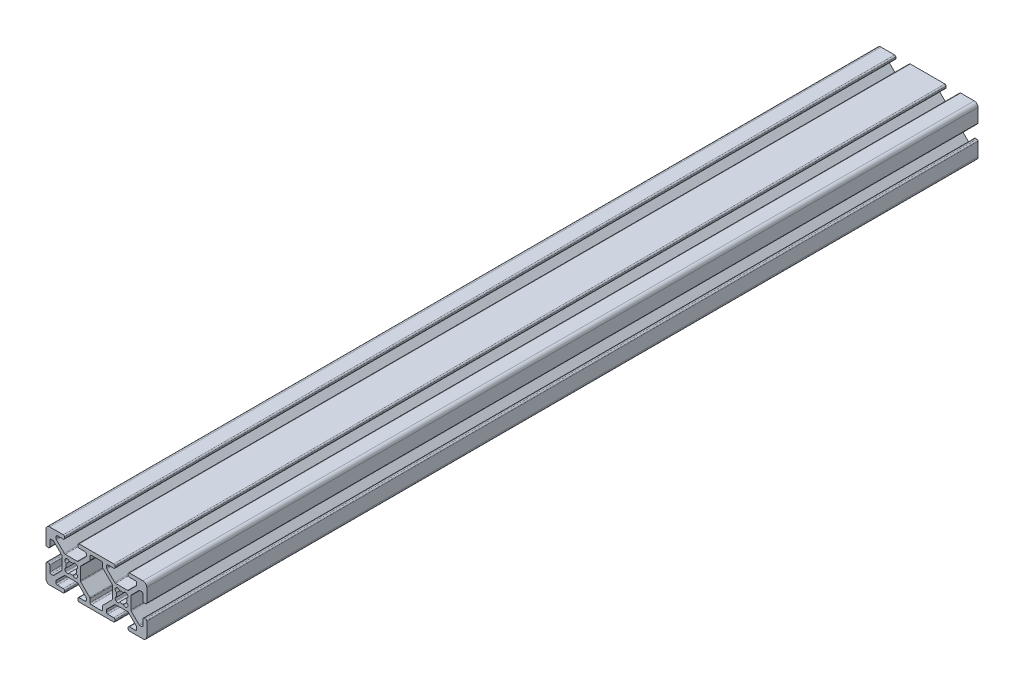
SolidWorks part; units mm, degrees
material "6105-T5 Aluminum"
ref_plane "Front Plane" through (0, 0, 0) normal (0, 0, 1) x (1, 0, 0)
ref_plane "Top Plane" through (0, 0, 0) normal (0, 1, 0) x (1, 0, 0)
ref_plane "Right Plane" through (0, 0, 0) normal (1, 0, 0) x (0, 0, -1)
sketch "Sketch1" plane through (0, 0, 0) normal (0, 0, 1) x (1, 0, 0)
  line L0 (-2.1249, -2.3045) -> (-2.3045, -2.1249)
  line L1 (-2.3045, 2.1249) -> (-2.1249, 2.3045)
  line L2 (2.1249, 2.3045) -> (2.3045, 2.1249)
  line L3 (2.3045, -2.1249) -> (2.1249, -2.3045)
  line L4 (-12.505, -7.992) -> (-12.505, -6.6448)
  line L5 (-12.6538, -6.2856) -> (-16.1962, -2.7431)
  line L6 (-16.345, -2.3839) -> (-16.345, 2.3839)
  line L7 (-16.1962, 2.7431) -> (-12.6538, 6.2856)
  line L8 (-12.505, 6.6448) -> (-12.505, 7.992)
  line L9 (-11.997, 8.5) -> (-8.003, 8.5)
  line L10 (-7.495, 7.992) -> (-7.495, 6.6448)
  line L11 (-7.3462, 6.2856) -> (-3.8038, 2.7431)
  line L12 (-3.655, 2.3839) -> (-3.655, -2.3839)
  line L13 (-3.8038, -2.7431) -> (-7.3462, -6.2856)
  line L14 (-7.495, -6.6448) -> (-7.495, -7.992)
  line L15 (-8.003, -8.5) -> (-11.997, -8.5)
  line L16 (-22.1249, -2.3045) -> (-22.3045, -2.1249)
  line L17 (-22.3045, 2.1249) -> (-22.1249, 2.3045)
  line L18 (-17.8751, 2.3045) -> (-17.6955, 2.1249)
  line L19 (-17.6955, -2.1249) -> (-17.8751, -2.3045)
  line L20 (-22.3839, -3.655) -> (-17.6161, -3.655)
  line L21 (-17.2569, -3.8038) -> (-14.1538, -6.9069)
  line L22 (-14.005, -7.2661) -> (-14.005, -7.992)
  line L23 (-14.513, -8.5) -> (-16.862, -8.5)
  line L24 (-17.37, -9.008) -> (-17.37, -9.492)
  line L25 (-16.862, -10) -> (-3.138, -10)
  line L26 (-2.63, -9.492) -> (-2.63, -9.008)
  line L27 (-3.138, -8.5) -> (-5.487, -8.5)
  line L28 (-5.995, -7.992) -> (-5.995, -7.2661)
  line L29 (-5.8462, -6.9069) -> (-2.7431, -3.8038)
  line L30 (-2.3839, -3.655) -> (2.3839, -3.655)
  line L31 (2.7431, -3.8038) -> (5.8462, -6.9069)
  line L32 (5.995, -7.2661) -> (5.995, -7.992)
  line L33 (5.487, -8.5) -> (3.138, -8.5)
  line L34 (2.63, -9.008) -> (2.63, -9.492)
  line L35 (3.138, -10) -> (8.5, -10)
  line L36 (10, -8.5) -> (10, -3.138)
  line L37 (9.492, -2.63) -> (9.008, -2.63)
  line L38 (8.5, -3.138) -> (8.5, -5.487)
  line L39 (7.992, -5.995) -> (7.2661, -5.995)
  line L40 (6.9069, -5.8462) -> (3.8038, -2.7431)
  line L41 (3.655, -2.3839) -> (3.655, 2.3839)
  line L42 (3.8038, 2.7431) -> (6.9069, 5.8462)
  line L43 (7.2661, 5.995) -> (7.992, 5.995)
  line L44 (8.5, 5.487) -> (8.5, 3.138)
  line L45 (9.008, 2.63) -> (9.492, 2.63)
  line L46 (10, 3.138) -> (10, 8.5)
  line L47 (8.5, 10) -> (3.138, 10)
  line L48 (2.63, 9.492) -> (2.63, 9.008)
  line L49 (3.138, 8.5) -> (5.487, 8.5)
  line L50 (5.995, 7.992) -> (5.995, 7.2661)
  line L51 (5.8462, 6.9069) -> (2.7431, 3.8038)
  line L52 (2.3839, 3.655) -> (-2.3839, 3.655)
  line L53 (-2.7431, 3.8038) -> (-5.8462, 6.9069)
  line L54 (-5.995, 7.2661) -> (-5.995, 7.992)
  line L55 (-5.487, 8.5) -> (-3.138, 8.5)
  line L56 (-2.63, 9.008) -> (-2.63, 9.492)
  line L57 (-3.138, 10) -> (-16.862, 10)
  line L58 (-17.37, 9.492) -> (-17.37, 9.008)
  line L59 (-16.862, 8.5) -> (-14.513, 8.5)
  line L60 (-14.005, 7.992) -> (-14.005, 7.2661)
  line L61 (-14.1538, 6.9069) -> (-17.2569, 3.8038)
  line L62 (-17.6161, 3.655) -> (-22.3839, 3.655)
  line L63 (-22.7431, 3.8038) -> (-25.8462, 6.9069)
  line L64 (-25.995, 7.2661) -> (-25.995, 7.992)
  line L65 (-25.487, 8.5) -> (-23.138, 8.5)
  line L66 (-22.63, 9.008) -> (-22.63, 9.492)
  line L67 (-23.138, 10) -> (-28.5, 10)
  line L68 (-30, 8.5) -> (-30, 3.138)
  line L69 (-29.492, 2.63) -> (-29.008, 2.63)
  line L70 (-28.5, 3.138) -> (-28.5, 5.487)
  line L71 (-27.992, 5.995) -> (-27.2661, 5.995)
  line L72 (-26.9069, 5.8462) -> (-23.8038, 2.7431)
  line L73 (-23.655, 2.3839) -> (-23.655, -2.3839)
  line L74 (-23.8038, -2.7431) -> (-26.9069, -5.8462)
  line L75 (-27.2661, -5.995) -> (-27.992, -5.995)
  line L76 (-28.5, -5.487) -> (-28.5, -3.138)
  line L77 (-29.008, -2.63) -> (-29.492, -2.63)
  line L78 (-30, -3.138) -> (-30, -8.5)
  line L79 (-28.5, -10) -> (-23.138, -10)
  line L80 (-22.63, -9.492) -> (-22.63, -9.008)
  line L81 (-23.138, -8.5) -> (-25.487, -8.5)
  line L82 (-25.995, -7.992) -> (-25.995, -7.2661)
  line L83 (-25.8462, -6.9069) -> (-22.7431, -3.8038)
  arc A0 (-1.9351, -0.804) -> (-2.3045, -2.1249) centre (-1.748, -1.5684) ccw
  arc A1 (-1.9351, 0.804) -> (-1.9351, -0.804) centre (0, 0) ccw
  arc A2 (-2.3045, 2.1249) -> (-1.9351, 0.804) centre (-1.748, 1.5684) ccw
  arc A3 (-0.804, 1.9351) -> (-2.1249, 2.3045) centre (-1.5684, 1.748) ccw
  arc A4 (0.804, 1.9351) -> (-0.804, 1.9351) centre (0, 0) ccw
  arc A5 (2.1249, 2.3045) -> (0.804, 1.9351) centre (1.5684, 1.748) ccw
  arc A6 (1.9351, 0.804) -> (2.3045, 2.1249) centre (1.748, 1.5684) ccw
  arc A7 (1.9351, -0.804) -> (1.9351, 0.804) centre (0, 0) ccw
  arc A8 (2.3045, -2.1249) -> (1.9351, -0.804) centre (1.748, -1.5684) ccw
  arc A9 (0.804, -1.9351) -> (2.1249, -2.3045) centre (1.5684, -1.748) ccw
  arc A10 (-0.804, -1.9351) -> (0.804, -1.9351) centre (0, 0) ccw
  arc A11 (-2.1249, -2.3045) -> (-0.804, -1.9351) centre (-1.5684, -1.748) ccw
  arc A12 (-12.505, -7.992) -> (-11.997, -8.5) centre (-11.997, -7.992) ccw
  arc A13 (-12.505, -6.6448) -> (-12.6538, -6.2856) centre (-13.013, -6.6448) ccw
  arc A14 (-16.345, -2.3839) -> (-16.1962, -2.7431) centre (-15.837, -2.3839) ccw
  arc A15 (-16.1962, 2.7431) -> (-16.345, 2.3839) centre (-15.837, 2.3839) ccw
  arc A16 (-12.6538, 6.2856) -> (-12.505, 6.6448) centre (-13.013, 6.6448) ccw
  arc A17 (-11.997, 8.5) -> (-12.505, 7.992) centre (-11.997, 7.992) ccw
  arc A18 (-7.495, 7.992) -> (-8.003, 8.5) centre (-8.003, 7.992) ccw
  arc A19 (-7.495, 6.6448) -> (-7.3462, 6.2856) centre (-6.987, 6.6448) ccw
  arc A20 (-3.655, 2.3839) -> (-3.8038, 2.7431) centre (-4.163, 2.3839) ccw
  arc A21 (-3.8038, -2.7431) -> (-3.655, -2.3839) centre (-4.163, -2.3839) ccw
  arc A22 (-7.3462, -6.2856) -> (-7.495, -6.6448) centre (-6.987, -6.6448) ccw
  arc A23 (-8.003, -8.5) -> (-7.495, -7.992) centre (-8.003, -7.992) ccw
  arc A24 (-21.9351, -0.804) -> (-22.3045, -2.1249) centre (-21.748, -1.5684) ccw
  arc A25 (-21.9351, 0.804) -> (-21.9351, -0.804) centre (-20, 0) ccw
  arc A26 (-22.3045, 2.1249) -> (-21.9351, 0.804) centre (-21.748, 1.5684) ccw
  arc A27 (-20.804, 1.9351) -> (-22.1249, 2.3045) centre (-21.5684, 1.748) ccw
  arc A28 (-19.196, 1.9351) -> (-20.804, 1.9351) centre (-20, 0) ccw
  arc A29 (-17.8751, 2.3045) -> (-19.196, 1.9351) centre (-18.4316, 1.748) ccw
  arc A30 (-18.0649, 0.804) -> (-17.6955, 2.1249) centre (-18.252, 1.5684) ccw
  arc A31 (-18.0649, -0.804) -> (-18.0649, 0.804) centre (-20, 0) ccw
  arc A32 (-17.6955, -2.1249) -> (-18.0649, -0.804) centre (-18.252, -1.5684) ccw
  arc A33 (-19.196, -1.9351) -> (-17.8751, -2.3045) centre (-18.4316, -1.748) ccw
  arc A34 (-20.804, -1.9351) -> (-19.196, -1.9351) centre (-20, 0) ccw
  arc A35 (-22.1249, -2.3045) -> (-20.804, -1.9351) centre (-21.5684, -1.748) ccw
  arc A36 (-22.3839, -3.655) -> (-22.7431, -3.8038) centre (-22.3839, -4.163) ccw
  arc A37 (-17.2569, -3.8038) -> (-17.6161, -3.655) centre (-17.6161, -4.163) ccw
  arc A38 (-14.005, -7.2661) -> (-14.1538, -6.9069) centre (-14.513, -7.2661) ccw
  arc A39 (-14.513, -8.5) -> (-14.005, -7.992) centre (-14.513, -7.992) ccw
  arc A40 (-16.862, -8.5) -> (-17.37, -9.008) centre (-16.862, -9.008) ccw
  arc A41 (-17.37, -9.492) -> (-16.862, -10) centre (-16.862, -9.492) ccw
  arc A42 (-3.138, -10) -> (-2.63, -9.492) centre (-3.138, -9.492) ccw
  arc A43 (-2.63, -9.008) -> (-3.138, -8.5) centre (-3.138, -9.008) ccw
  arc A44 (-5.995, -7.992) -> (-5.487, -8.5) centre (-5.487, -7.992) ccw
  arc A45 (-5.8462, -6.9069) -> (-5.995, -7.2661) centre (-5.487, -7.2661) ccw
  arc A46 (-2.3839, -3.655) -> (-2.7431, -3.8038) centre (-2.3839, -4.163) ccw
  arc A47 (2.7431, -3.8038) -> (2.3839, -3.655) centre (2.3839, -4.163) ccw
  arc A48 (5.995, -7.2661) -> (5.8462, -6.9069) centre (5.487, -7.2661) ccw
  arc A49 (5.487, -8.5) -> (5.995, -7.992) centre (5.487, -7.992) ccw
  arc A50 (3.138, -8.5) -> (2.63, -9.008) centre (3.138, -9.008) ccw
  arc A51 (2.63, -9.492) -> (3.138, -10) centre (3.138, -9.492) ccw
  arc A52 (8.5, -10) -> (10, -8.5) centre (8.5, -8.5) ccw
  arc A53 (10, -3.138) -> (9.492, -2.63) centre (9.492, -3.138) ccw
  arc A54 (9.008, -2.63) -> (8.5, -3.138) centre (9.008, -3.138) ccw
  arc A55 (7.992, -5.995) -> (8.5, -5.487) centre (7.992, -5.487) ccw
  arc A56 (6.9069, -5.8462) -> (7.2661, -5.995) centre (7.2661, -5.487) ccw
  arc A57 (3.655, -2.3839) -> (3.8038, -2.7431) centre (4.163, -2.3839) ccw
  arc A58 (3.8038, 2.7431) -> (3.655, 2.3839) centre (4.163, 2.3839) ccw
  arc A59 (7.2661, 5.995) -> (6.9069, 5.8462) centre (7.2661, 5.487) ccw
  arc A60 (8.5, 5.487) -> (7.992, 5.995) centre (7.992, 5.487) ccw
  arc A61 (8.5, 3.138) -> (9.008, 2.63) centre (9.008, 3.138) ccw
  arc A62 (9.492, 2.63) -> (10, 3.138) centre (9.492, 3.138) ccw
  arc A63 (10, 8.5) -> (8.5, 10) centre (8.5, 8.5) ccw
  arc A64 (3.138, 10) -> (2.63, 9.492) centre (3.138, 9.492) ccw
  arc A65 (2.63, 9.008) -> (3.138, 8.5) centre (3.138, 9.008) ccw
  arc A66 (5.995, 7.992) -> (5.487, 8.5) centre (5.487, 7.992) ccw
  arc A67 (5.8462, 6.9069) -> (5.995, 7.2661) centre (5.487, 7.2661) ccw
  arc A68 (2.3839, 3.655) -> (2.7431, 3.8038) centre (2.3839, 4.163) ccw
  arc A69 (-2.7431, 3.8038) -> (-2.3839, 3.655) centre (-2.3839, 4.163) ccw
  arc A70 (-5.995, 7.2661) -> (-5.8462, 6.9069) centre (-5.487, 7.2661) ccw
  arc A71 (-5.487, 8.5) -> (-5.995, 7.992) centre (-5.487, 7.992) ccw
  arc A72 (-3.138, 8.5) -> (-2.63, 9.008) centre (-3.138, 9.008) ccw
  arc A73 (-2.63, 9.492) -> (-3.138, 10) centre (-3.138, 9.492) ccw
  arc A74 (-16.862, 10) -> (-17.37, 9.492) centre (-16.862, 9.492) ccw
  arc A75 (-17.37, 9.008) -> (-16.862, 8.5) centre (-16.862, 9.008) ccw
  arc A76 (-14.005, 7.992) -> (-14.513, 8.5) centre (-14.513, 7.992) ccw
  arc A77 (-14.1538, 6.9069) -> (-14.005, 7.2661) centre (-14.513, 7.2661) ccw
  arc A78 (-17.6161, 3.655) -> (-17.2569, 3.8038) centre (-17.6161, 4.163) ccw
  arc A79 (-22.7431, 3.8038) -> (-22.3839, 3.655) centre (-22.3839, 4.163) ccw
  arc A80 (-25.995, 7.2661) -> (-25.8462, 6.9069) centre (-25.487, 7.2661) ccw
  arc A81 (-25.487, 8.5) -> (-25.995, 7.992) centre (-25.487, 7.992) ccw
  arc A82 (-23.138, 8.5) -> (-22.63, 9.008) centre (-23.138, 9.008) ccw
  arc A83 (-22.63, 9.492) -> (-23.138, 10) centre (-23.138, 9.492) ccw
  arc A84 (-28.5, 10) -> (-30, 8.5) centre (-28.5, 8.5) ccw
  arc A85 (-30, 3.138) -> (-29.492, 2.63) centre (-29.492, 3.138) ccw
  arc A86 (-29.008, 2.63) -> (-28.5, 3.138) centre (-29.008, 3.138) ccw
  arc A87 (-27.992, 5.995) -> (-28.5, 5.487) centre (-27.992, 5.487) ccw
  arc A88 (-26.9069, 5.8462) -> (-27.2661, 5.995) centre (-27.2661, 5.487) ccw
  arc A89 (-23.655, 2.3839) -> (-23.8038, 2.7431) centre (-24.163, 2.3839) ccw
  arc A90 (-23.8038, -2.7431) -> (-23.655, -2.3839) centre (-24.163, -2.3839) ccw
  arc A91 (-27.2661, -5.995) -> (-26.9069, -5.8462) centre (-27.2661, -5.487) ccw
  arc A92 (-28.5, -5.487) -> (-27.992, -5.995) centre (-27.992, -5.487) ccw
  arc A93 (-28.5, -3.138) -> (-29.008, -2.63) centre (-29.008, -3.138) ccw
  arc A94 (-29.492, -2.63) -> (-30, -3.138) centre (-29.492, -3.138) ccw
  arc A95 (-30, -8.5) -> (-28.5, -10) centre (-28.5, -8.5) ccw
  arc A96 (-23.138, -10) -> (-22.63, -9.492) centre (-23.138, -9.492) ccw
  arc A97 (-22.63, -9.008) -> (-23.138, -8.5) centre (-23.138, -9.008) ccw
  arc A98 (-25.995, -7.992) -> (-25.487, -8.5) centre (-25.487, -7.992) ccw
  arc A99 (-25.8462, -6.9069) -> (-25.995, -7.2661) centre (-25.487, -7.2661) ccw
extrude "Extrude1" add sketch "Sketch1" against normal blind 330
